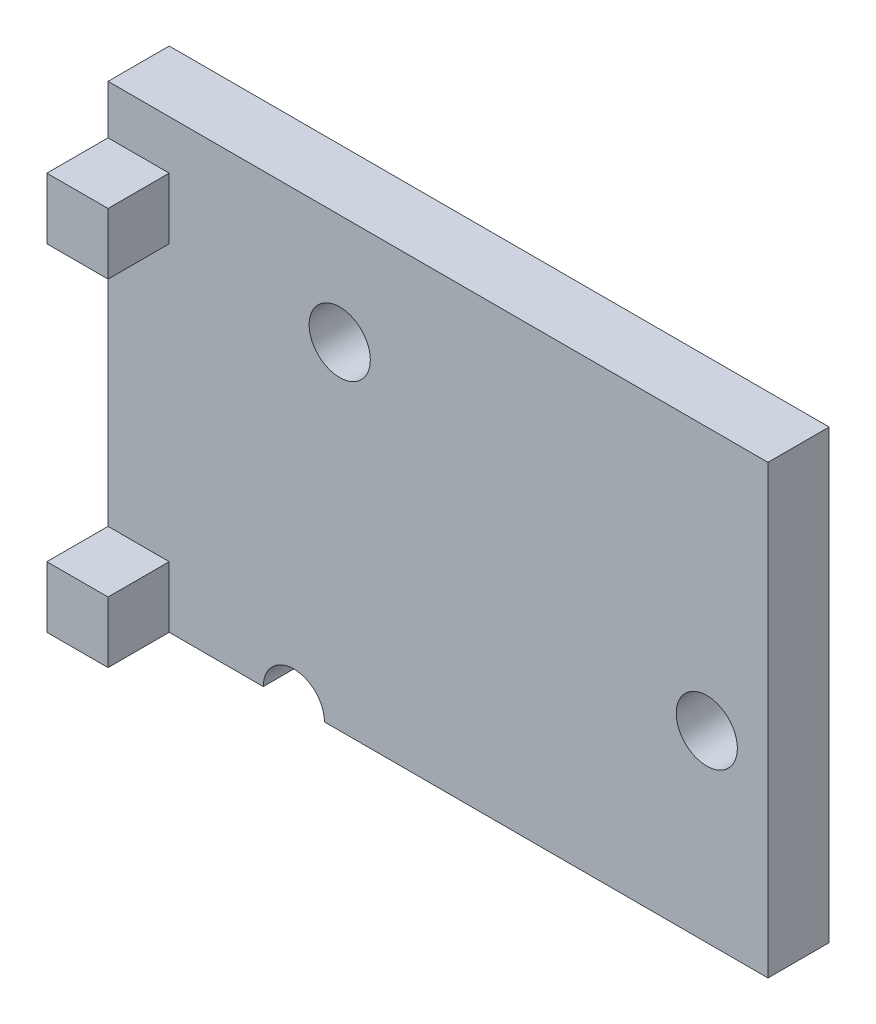
SolidWorks part; units mm, degrees
ref_plane "Front Plane" through (0, 0, 0) normal (0, 0, 1) x (1, 0, 0)
ref_plane "Top Plane" through (0, 0, 0) normal (0, 1, 0) x (1, 0, 0)
ref_plane "Right Plane" through (0, 0, 0) normal (1, 0, 0) x (0, 0, -1)
sketch "Sketch1" plane through (0, 0, 0) normal (0, 0, 1) x (1, 0, 0)
  line L0 (-3.75, -3.25) -> (-4.5, -3.25)
  line L1 (4.5, 3.25) -> (-4.5, 3.25)
  line L2 (4.5, 3.25) -> (4.5, -3.25)
  line L3 (4.5, -3.25) -> (-2.75, -3.25)
  line L4 (-4.5, 3.25) -> (-4.5, -3.25)
  line L5 (4.5, 3.25) -> (-4.5, -3.25) construction
  line L6 (4.5, -3.25) -> (-4.5, 3.25) construction
  circle A0 centre (-2.5, 2.25) radius 0.5
  circle A1 centre (3.5, -0.25) radius 0.5
  arc A2 (-2.75, -3.25) -> (-3.75, -3.25) centre (-3.25, -3.25) ccw
  point P0 (0, 0)
  dimension "D3" = 1
  dimension "D4" = 1
  dimension "D5" = 2
  dimension "D6" = 1
  dimension "D7" = 3
  dimension "D1" = 9
  dimension "D2" = 6.5
  dimension "D8" = 7.75
extrude "Front Face Ext" add sketch "Sketch1" along normal blind 1
sketch "Sketch2" plane through (-4.5, 0, 0) normal (-1, 0, 0) x (0, 0, 1)
  line L1 (0, 3.25) -> (1, 3.25)
  line L2 (0, 3.25) -> (0, -3.25)
  line L3 (0, -3.25) -> (1, -3.25)
  line L4 (1, 3.25) -> (1, -3.25)
extrude "Boss-Extrude1" add sketch "Sketch2" along normal blind 1.7874
sketch "Sketch3" plane through (0, 0, 1) normal (0, 0, 1) x (1, 0, 0)
  line L2 (-6.2874, 3.25) -> (-5.2874, 3.25)
  line L3 (-6.2874, 3.25) -> (-6.2874, 2.25)
  line L4 (-6.2874, 2.25) -> (-5.2874, 2.25)
  line L5 (-5.2874, 3.25) -> (-5.2874, 2.25)
  line L6 (-6.2874, -3.25) -> (-5.2874, -3.25)
  line L7 (-6.2874, -3.25) -> (-6.2874, -2.25)
  line L8 (-6.2874, -2.25) -> (-5.2874, -2.25)
  line L9 (-5.2874, -3.25) -> (-5.2874, -2.25)
  dimension "D1" = 1
  dimension "D2" = 1
extrude "Boss-Extrude2" add sketch "Sketch3" along normal blind 1
sketch "Sketch4" plane through (0, 3.25, 0) normal (0, 1, 0) x (1, 0, 0)
  line L1 (4.5, -1) -> (-6.2874, -1)
  line L2 (4.5, -1) -> (4.5, 0)
  line L3 (4.5, 0) -> (-6.2874, 0)
  line L4 (-6.2874, -1) -> (-6.2874, 0)
extrude "Boss-Extrude3" add sketch "Sketch4" along normal blind 0.8
